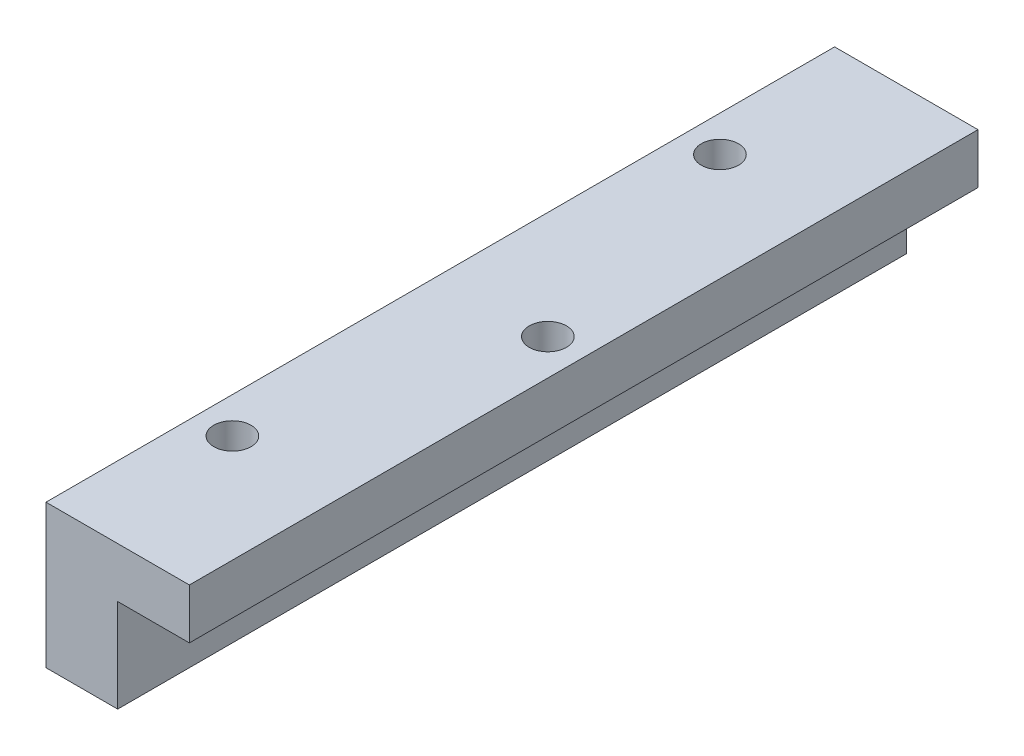
SolidWorks part; units mm, degrees
ref_plane "Front Plane" through (0, 0, 0) normal (0, 0, 1) x (1, 0, 0)
ref_plane "Top Plane" through (0, 0, 0) normal (0, 1, 0) x (1, 0, 0)
ref_plane "Right Plane" through (0, 0, 0) normal (1, 0, 0) x (0, 0, -1)
sketch "Sketch1" plane through (0, 0, 0) normal (0, 0, 1) x (1, 0, 0)
  line L1 (0, 0) -> (10, 0)
  line L2 (0, 0) -> (0, 20)
  line L3 (0, 20) -> (10, 20)
  line L4 (10, 0) -> (10, 13)
  line L5 (10, 20) -> (20, 20)
  line L7 (10, 13) -> (20, 13)
  line L8 (20, 20) -> (20, 13)
  dimension "D1" = 10
  dimension "D2" = 20
  dimension "D3" = 10
  dimension "D4" = 7
extrude "Boss-Extrude1" add sketch "Sketch1" along normal blind 110
sketch "Sketch2" plane through (0, 20, 0) normal (0, 1, 0) x (1, 0, 0)
  line L0 (5, 0) -> (5, -110) construction
  line L1 (20, 0) -> (0, 0) construction
  line L2 (20, -110) -> (0, -110) construction
  line L3 (0, -110) -> (0, 0) construction
  circle A0 centre (5, -21) radius 2.6
  circle A1 centre (5, -89) radius 2.6
  point P12 (5, -55)
  dimension "D2" = 5.2
  dimension "D1" = 5
  dimension "D3" = 34
  dimension "D4" = 34
extrude "Cut-Extrude1" cut sketch "Sketch2" against normal blind 110
sketch "Sketch3" plane through (0, 20, 0) normal (0, 1, 0) x (1, 0, 0)
  line L0 (0, -55) -> (20, -55) construction
  line L1 (0, -110) -> (0, 0) construction
  line L2 (20, -110) -> (20, 0) construction
  line L4 (15, -50.4389) -> (11.05, -52.7195)
  line L5 (11.05, -52.7195) -> (11.05, -57.2805)
  line L6 (11.05, -57.2805) -> (15, -59.5611)
  line L7 (15, -59.5611) -> (18.95, -57.2805)
  line L8 (18.95, -57.2805) -> (18.95, -52.7195)
  line L9 (18.95, -52.7195) -> (15, -50.4389)
  circle A0 centre (15, -55) radius 3.95 construction
  dimension "D1" = 7.9
  dimension "D2" = 5
extrude "Cut-Extrude2" cut sketch "Sketch3" along normal blind 3 from surface at -7 starting at face at (15, 13, 55)
sketch "Sketch4" plane through (0, 16, 0) normal (0, -1, 0) x (1, 0, 0)
  line L0 (15, 59.5611) -> (15, 50.4389) construction
  circle A0 centre (15, 55) radius 2.6
  dimension "D1" = 5.2
extrude "Cut-Extrude3" cut sketch "Sketch4" against normal blind 13
